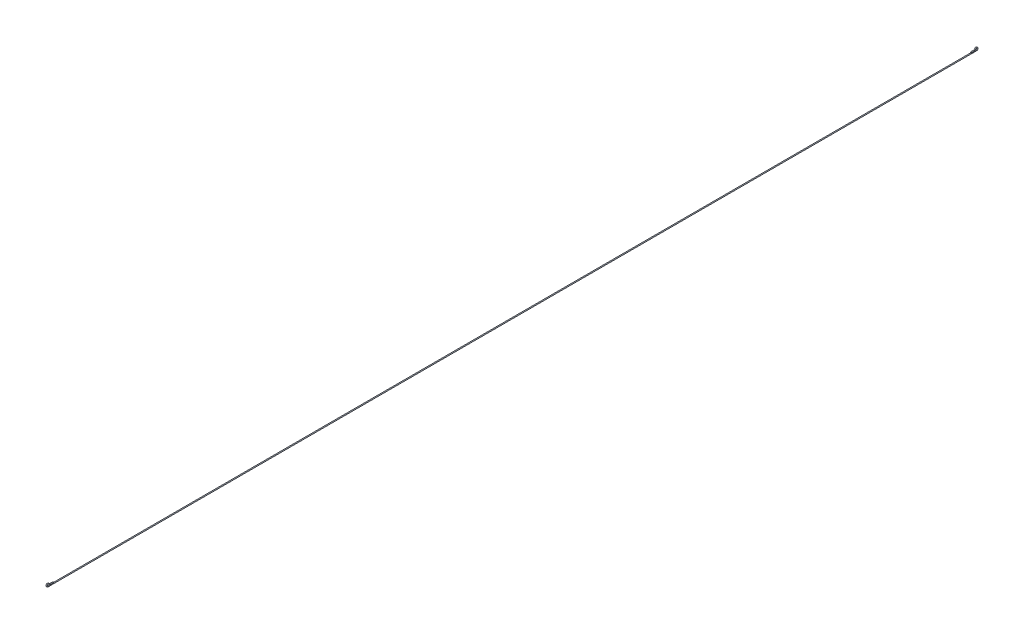
SolidWorks part; units mm, degrees
ref_plane "Front Plane" through (0, 0, 0) normal (0, 0, 1) x (1, 0, 0)
ref_plane "Top Plane" through (0, 0, 0) normal (0, 1, 0) x (1, 0, 0)
ref_plane "Right Plane" through (0, 0, 0) normal (1, 0, 0) x (0, 0, -1)
sketch "Sketch1" plane through (0, 0, 0) normal (0, 0, 1) x (1, 0, 0)
  circle A0 centre (0, 0) radius 1.5
  dimension "D1" = 3
sketch "Sketch2" plane through (0, 0, 0) normal (1, 0, 0) x (0, 0, -1)
  line L0 (-17.4162, -3) -> (1555.5838, -3)
  line L1 (-10, 0) -> (0, 0)
  arc A0 (-17.4162, -3) -> (-13.7081, 2.5) centre (-17.4162, 1) cw
  arc A1 (-13.7081, 2.5) -> (-10, 0) centre (-10, 4) ccw
  dimension "D3" = 4
  dimension "D4" = 4
  dimension "D1" = 1573
  dimension "D2" = 10
  dimension "D5" = 3
sweep "Sweep1" add profiles "Sketch1" path "Sketch2"
mirror "Mirror1" about plane through (0, -3, -1555.5838) normal (0, 0, -1) of "Sweep1"
